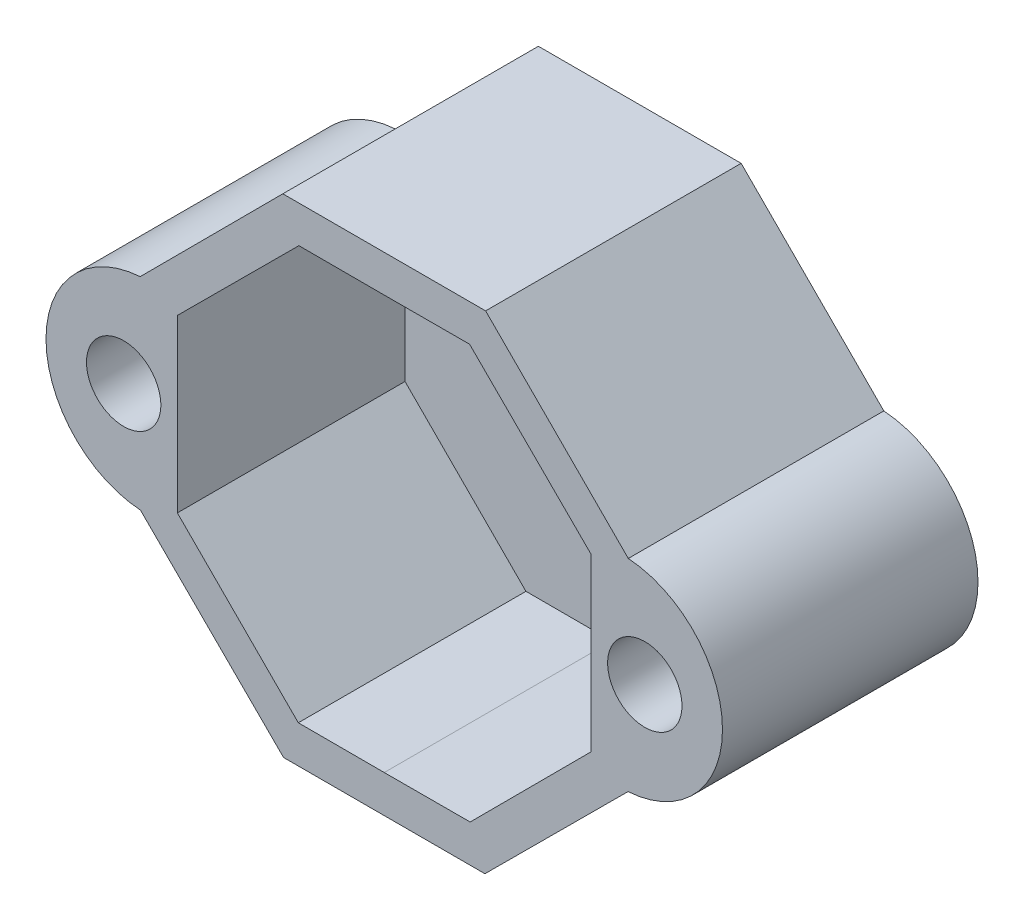
SolidWorks part; units mm, degrees
ref_plane "Front Plane" through (0, 0, 0) normal (0, 0, 1) x (1, 0, 0)
ref_plane "Top Plane" through (0, 0, 0) normal (0, 1, 0) x (1, 0, 0)
ref_plane "Right Plane" through (0, 0, 0) normal (1, 0, 0) x (0, 0, -1)
ref_plane "Plane1" through (0, 0, 11) normal (0, 0, 1) x (1, 0, 0)
sketch "Sketch1" plane through (0, 0, 11) normal (0, 0, 1) x (1, 0, 0)
  line L2 (4.334, -10.5063) -> (10.4937, -4.3645)
  line L3 (0, 8.9) -> (3.6735, 8.9054)
  line L4 (4.3645, 10.4937) -> (10.5063, 4.334)
  line L5 (3.6735, 8.9054) -> (8.8946, 3.6994)
  line L6 (8.8946, 3.6994) -> (8.9054, -3.6735)
  line L7 (8.9054, -3.6735) -> (3.6994, -8.8946)
  line L8 (3.6994, -8.8946) -> (0, -8.9)
  line L11 (-4.3645, 10.4937) -> (4.3645, 10.4937)
  line L12 (-4.334, -10.5063) -> (4.334, -10.5063)
  line L14 (0, 0) -> (0, 2.6737) construction
  line L15 (0, 0) -> (0, -12.0874) construction
  line L16 (0, 0) -> (0, 14.5338) construction
  line L17 (0, 8.9) -> (-3.6735, 8.9054)
  line L18 (-4.3645, 10.4937) -> (-10.5063, 4.334)
  line L19 (-3.6735, 8.9054) -> (-8.8946, 3.6994)
  line L20 (-8.8946, 3.6994) -> (-8.9054, -3.6735)
  line L21 (-4.334, -10.5063) -> (-10.4937, -4.3645)
  line L22 (-8.9054, -3.6735) -> (-3.6994, -8.8946)
  line L23 (-3.6994, -8.8946) -> (0, -8.9)
  arc A1 (10.5063, 4.334) -> (10.4937, -4.3645) centre (10.2009, -0.0148) cw
  circle A3 centre (11.2172, -0.0089) radius 1.6
  circle A4 centre (-11.2172, -0.0089) radius 1.6
  arc A5 (-10.5063, 4.334) -> (-10.4937, -4.3645) centre (-10.2009, -0.0148) ccw
  point P5 (0, 10.4937)
  point P26 (0, -10.5063)
extrude "Boss-Extrude1" add sketch "Sketch1" against normal blind 9.8
sketch "Sketch2" plane through (0, 0, 1.2) normal (0, 0, -1) x (-1, 0, 0)
  line L245 (4.3645, 10.4937) -> (-4.3645, 10.4937)
  line L246 (10.5063, 4.334) -> (4.3645, 10.4937)
  line L247 (4.334, -10.5063) -> (10.4937, -4.3645)
  line L248 (-4.334, -10.5063) -> (4.334, -10.5063)
  line L249 (-10.4937, -4.3645) -> (-4.334, -10.5063)
  line L250 (-4.3645, 10.4937) -> (-10.5063, 4.334)
  circle A50 centre (0, 0) radius 3.95
  arc A54 (10.4937, -4.3645) -> (10.5063, 4.334) centre (10.2009, -0.0148) ccw
  arc A55 (-10.5063, 4.334) -> (-10.4937, -4.3645) centre (-10.2009, -0.0148) ccw
extrude "Boss-Extrude2" add sketch "Sketch2" along normal blind 1.2
